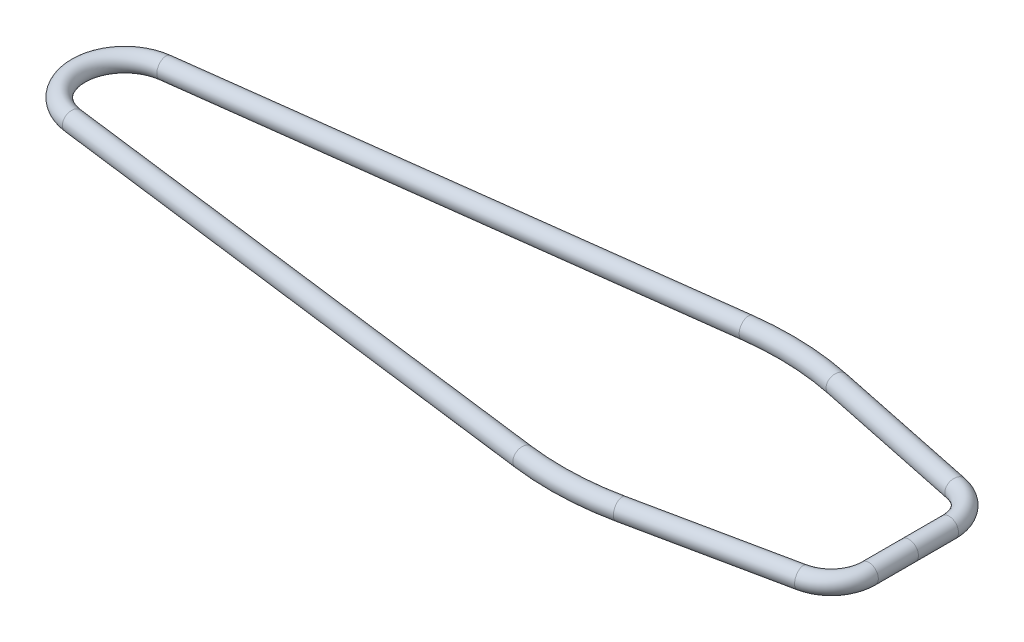
SolidWorks part; units mm, degrees
material "6061-T6 (SS)"
ref_plane "Front Plane" through (0, 0, 0) normal (0, 0, 1) x (1, 0, 0)
ref_plane "Top Plane" through (0, 0, 0) normal (0, 1, 0) x (1, 0, 0)
ref_plane "Right Plane" through (0, 0, 0) normal (1, 0, 0) x (0, 0, -1)
sketch "Sketch1" plane through (0, 0, 0) normal (0, 1, 0) x (1, 0, 0)
  line L0 (-7.9065, 61.9125) -> (686.9853, 150.6536)
  line L1 (812.9555, 145.7144) -> (1014.7456, 103.6748)
  line L2 (1055.1847, 53.9426) -> (1055.1847, -53.9426)
  line L3 (1014.7456, -103.6748) -> (812.9555, -145.7144)
  line L4 (686.9853, -150.6536) -> (-7.9065, -61.9125)
  arc A0 (-7.9065, 61.9125) -> (-7.9065, -61.9125) centre (0, 0) ccw
  arc A1 (812.9555, -145.7144) -> (686.9853, -150.6536) centre (735.2489, 227.2771) cw
  arc A2 (686.9853, 150.6536) -> (812.9555, 145.7144) centre (735.2489, -227.2771) cw
  arc A3 (1055.1847, -53.9426) -> (1014.7456, -103.6748) centre (1004.3847, -53.9426) cw
  arc A4 (1014.7456, 103.6748) -> (1055.1847, 53.9426) centre (1004.3847, 53.9426) cw
  point P9 (-62.4153, 0)
  point P13 (750.3847, -158.75)
  point P16 (750.3847, 158.75)
  point P19 (1055.1847, -95.25)
  point P22 (1055.1847, 95.25)
  dimension "D6" = 381
  dimension "D7" = 50.8
  dimension "D1" = 123.825
  dimension "D2" = 304.8
  dimension "D3" = 190.5
  dimension "D4" = 1117.6
  dimension "D5" = 317.5
sketch "Sketch2" plane through (0, 0, 0) normal (0, 0, 1) x (1, 0, 0)
  circle A0 centre (1055.1847, 0) radius 12.7
  circle A1 centre (1055.1847, 0) radius 11.1125
  dimension "D1" = 25.4
  dimension "D2" = 1.5875
sweep "Sweep1" add profiles "Sketch2" path "Sketch1"
